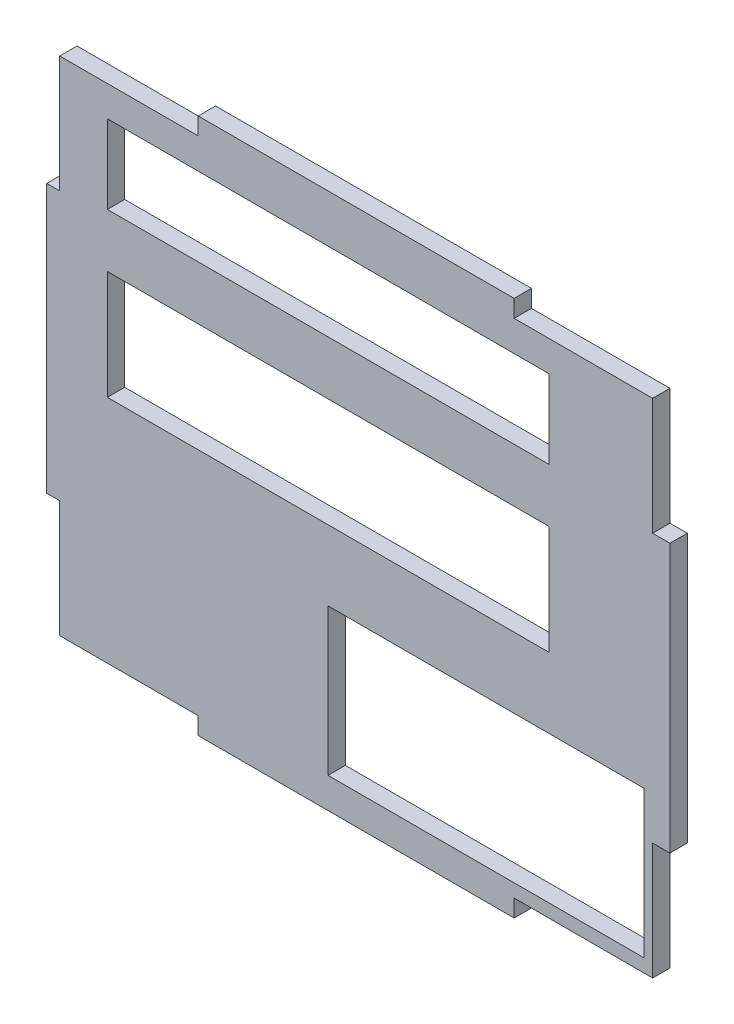
SolidWorks part; units mm, degrees
ref_plane "正面" through (0, 0, 0) normal (0, 0, 1) x (1, 0, 0)
ref_plane "平面" through (0, 0, 0) normal (0, 1, 0) x (1, 0, 0)
ref_plane "右側面" through (0, 0, 0) normal (1, 0, 0) x (0, 0, -1)
sketch "ｽｹｯﾁ1" plane through (0, 0, 0) normal (0, 0, 1) x (1, 0, 0)
  line L1 (-37.0426, 40.7363) -> (34.9574, 40.7363)
  line L2 (-37.0426, 40.7363) -> (-37.0426, -21.2637)
  line L3 (-37.0426, -21.2637) -> (34.9574, -21.2637)
  line L4 (34.9574, 40.7363) -> (34.9574, -21.2637)
  dimension "D1" = 72
  dimension "D2" = 62
extrude "ﾎﾞｽ - 押し出し1" add sketch "ｽｹｯﾁ1" along normal blind 2
sketch "ｽｹｯﾁ2" plane through (0, 0, 2) normal (0, 0, 1) x (1, 0, 0)
  line L0 (32.9574, 38.7363) -> (16.9574, 38.7363) construction
  line L1 (34.9574, 40.7363) -> (16.9574, 40.7363)
  line L2 (34.9574, 40.7363) -> (34.9574, 38.7363)
  line L3 (34.9574, 38.7363) -> (16.9574, 38.7363)
  line L4 (16.9574, 40.7363) -> (16.9574, 38.7363)
  line L5 (-35.5426, -19.2637) -> (-19.5426, -19.2637) construction
  line L6 (-37.5426, 40.7363) -> (-19.5426, 40.7363)
  line L7 (-37.5426, 40.7363) -> (-37.5426, 38.7363)
  line L8 (-37.5426, 38.7363) -> (-19.5426, 38.7363)
  line L9 (-19.5426, 40.7363) -> (-19.5426, 38.7363)
  line L10 (-37.5426, -21.2637) -> (-19.5426, -21.2637)
  line L11 (-37.5426, -21.2637) -> (-37.5426, -19.2637)
  line L12 (-37.5426, -19.2637) -> (-19.5426, -19.2637)
  line L13 (-19.5426, -21.2637) -> (-19.5426, -19.2637)
  line L15 (34.9574, -21.2637) -> (16.9574, -21.2637)
  line L16 (34.9574, -21.2637) -> (34.9574, -19.2637)
  line L17 (34.9574, -19.2637) -> (16.9574, -19.2637)
  line L18 (16.9574, -21.2637) -> (16.9574, -19.2637)
  dimension "D1" = 18
  dimension "D2" = 18
  dimension "D3" = 18
  dimension "D4" = 18
extrude "ｶｯﾄ - 押し出し1" cut sketch "ｽｹｯﾁ2" against normal through all contours L4 L3 L2 L1 | L8 L9 L6 L7 | L12 L13 L10 L11 | L15 L18 L17 L16
sketch "ｽｹｯﾁ3" plane through (0, 0, 2) normal (0, 0, 1) x (1, 0, 0)
  line L0 (32.9574, -21.2637) -> (32.9574, -5.7637) construction
  line L1 (34.9574, 40.7363) -> (32.9574, 40.7363)
  line L2 (34.9574, 40.7363) -> (34.9574, 25.2363)
  line L3 (34.9574, 25.2363) -> (32.9574, 25.2363)
  line L4 (32.9574, 40.7363) -> (32.9574, 25.2363)
  line L5 (-35.5426, -21.2637) -> (-35.5426, -5.7637) construction
  line L6 (34.9574, -21.2637) -> (32.9574, -21.2637)
  line L7 (34.9574, -21.2637) -> (34.9574, -5.7637)
  line L8 (34.9574, -5.7637) -> (32.9574, -5.7637)
  line L9 (32.9574, -21.2637) -> (32.9574, -5.7637)
  line L10 (-37.5426, -21.2637) -> (-35.5426, -21.2637)
  line L11 (-37.5426, -21.2637) -> (-37.5426, -5.7637)
  line L12 (-37.5426, -5.7637) -> (-35.5426, -5.7637)
  line L13 (-35.5426, -21.2637) -> (-35.5426, -5.7637)
  line L15 (-37.5426, 40.7363) -> (-35.5426, 40.7363)
  line L16 (-37.5426, 40.7363) -> (-37.5426, 25.2363)
  line L17 (-37.5426, 25.2363) -> (-35.5426, 25.2363)
  line L18 (-35.5426, 40.7363) -> (-35.5426, 25.2363)
  dimension "D1" = 15.5
  dimension "D2" = 15.5
  dimension "D3" = 15.5
  dimension "D4" = 15.5
extrude "ｶｯﾄ - 押し出し2" cut sketch "ｽｹｯﾁ3" against normal through all
sketch "ｽｹｯﾁ4" plane through (0, 0, 2) normal (0, 0, 1) x (1, 0, 0)
  line L0 (-30.0426, -0.8637) -> (-30.0426, 29.1363) construction
  line L1 (31.9574, -17.7397) -> (-4.5426, -17.7397)
  line L2 (31.9574, -17.7397) -> (31.9574, -0.7842)
  line L3 (31.9574, -0.7842) -> (-4.5426, -0.7842)
  line L4 (-4.5426, -17.7397) -> (-4.5426, -0.7842)
  line L5 (20.9574, 7.3363) -> (-30.0426, 7.3363)
  line L6 (20.9574, 7.3363) -> (20.9574, 19.9326)
  line L7 (20.9574, 19.9326) -> (-30.0426, 19.9326)
  line L8 (-30.0426, 7.3363) -> (-30.0426, 19.9326)
  line L10 (20.9574, 26.1363) -> (-30.0426, 26.1363)
  line L11 (20.9574, 26.1363) -> (20.9574, 35.2113)
  line L12 (20.9574, 35.2113) -> (-30.0426, 35.2113)
  line L13 (-30.0426, 26.1363) -> (-30.0426, 35.2113)
extrude "ｶｯﾄ - 押し出し3" cut sketch "ｽｹｯﾁ4" against normal through all
